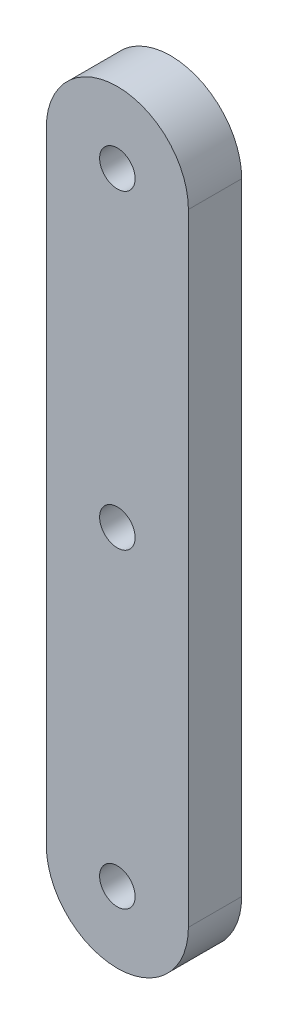
SolidWorks part; units mm, degrees
ref_plane "Front Plane" through (0, 0, 0) normal (0, 0, 1) x (1, 0, 0)
ref_plane "Top Plane" through (0, 0, 0) normal (0, 1, 0) x (1, 0, 0)
ref_plane "Right Plane" through (0, 0, 0) normal (1, 0, 0) x (0, 0, -1)
sketch "Model" plane through (0, 0, 0) normal (0, 0, 1) x (1, 0, 0)
  line L0 (31.7937, 45.6899) -> (31.7937, 10.6899)
  line L1 (39.7937, 10.6899) -> (39.7937, 45.6899)
  arc A0 (39.7937, 45.6899) -> (31.7937, 45.6899) centre (35.7937, 45.6899) ccw
  arc A1 (31.7937, 10.6899) -> (39.7937, 10.6899) centre (35.7937, 10.6899) ccw
  circle A2 centre (35.7937, 10.6899) radius 1
  circle A3 centre (35.7937, 45.6899) radius 1
  circle A4 centre (35.7937, 28.1899) radius 1
extrude "Boss-Extrude1" add sketch "Model" along normal blind 3 contours A3 | A2 | A4 | L0 A1 L1 A0
